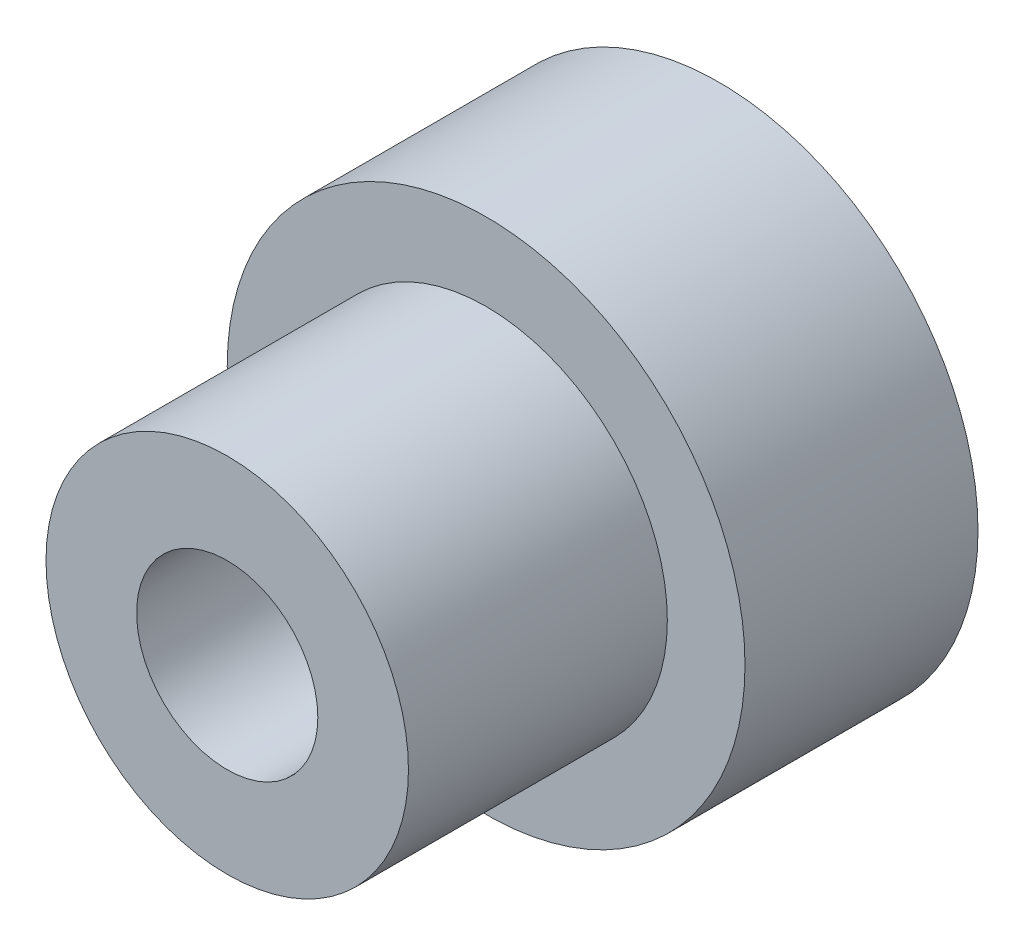
SolidWorks part; units mm, degrees
material "Тефлон"
ref_plane "Спереди" through (0, 0, 0) normal (0, 0, 1) x (1, 0, 0)
ref_plane "Сверху" through (0, 0, 0) normal (0, 1, 0) x (1, 0, 0)
ref_plane "Справа" through (0, 0, 0) normal (1, 0, 0) x (0, 0, -1)
sketch "Эскиз2" plane through (0, 0, 0) normal (0, 0, 1) x (1, 0, 0)
  circle A0 centre (0, 0) radius 7
  dimension "D1" = 14
extrude "Бобышка-Вытянуть1" add sketch "Эскиз2" along normal blind 10
sketch "Эскиз3" plane through (0, 0, 0) normal (0, 0, -1) x (-1, 0, 0)
  circle A0 centre (0, 0) radius 10
  dimension "D1" = 20
extrude "Бобышка-Вытянуть2" add sketch "Эскиз3" along normal blind 9
sketch "Эскиз4" plane through (0, 0, 10) normal (0, 0, 1) x (1, 0, 0)
  circle A0 centre (0, 0) radius 3.5
  dimension "D1" = 7
extrude "Вырез-Вытянуть1" cut sketch "Эскиз4" against normal through all
sketch "Эскиз5" plane through (0, 0, 10) normal (0, 0, 1) x (1, 0, 0)
  circle A0 centre (0, 0) radius 5.5
  dimension "D1" = 11
extrude "Вырез-Вытянуть2" cut sketch "Эскиз5" against normal blind 2.5 from offset 13
